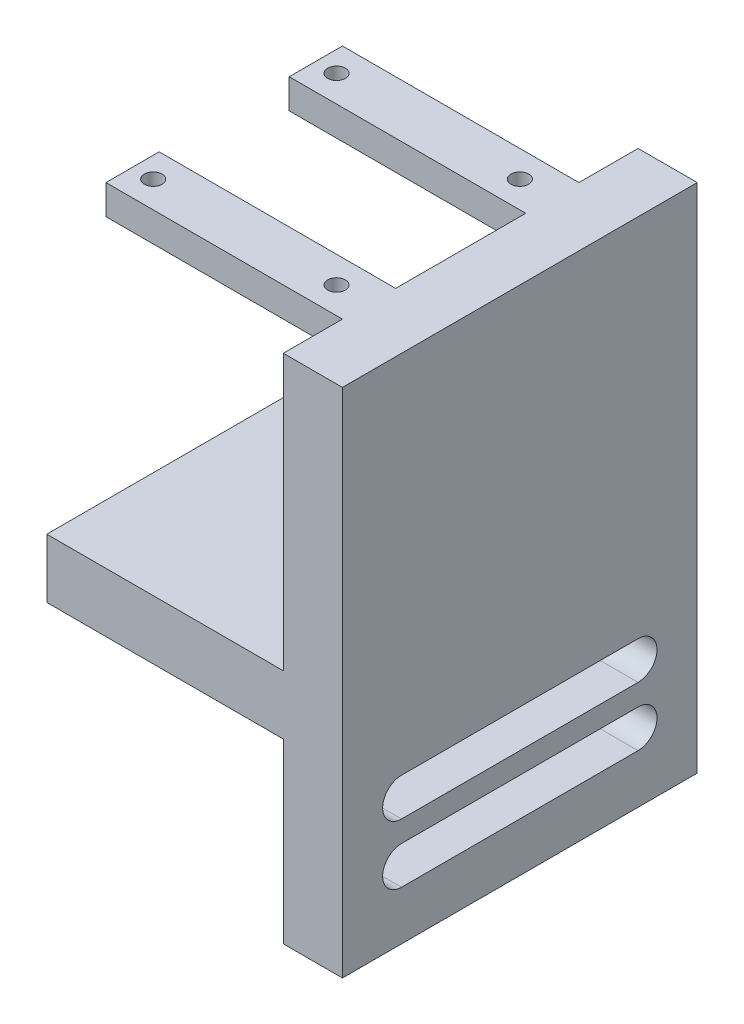
SolidWorks part; units mm, degrees
ref_plane "Front Plane" through (0, 0, 0) normal (0, 0, 1) x (1, 0, 0)
ref_plane "Top Plane" through (0, 0, 0) normal (0, 1, 0) x (1, 0, 0)
ref_plane "Right Plane" through (0, 0, 0) normal (1, 0, 0) x (0, 0, -1)
sketch "Sketch1" plane through (0, 0, 0) normal (1, 0, 0) x (0, 0, -1)
  line L0 (0, 2.75) -> (0, -2.75) construction
  line L5 (-30, 56.5) -> (30, 56.5)
  line L6 (-30, 56.5) -> (-30, 0)
  line L7 (-30, 0) -> (30, 0)
  line L8 (30, 56.5) -> (30, 0)
  line L9 (-30, 56.5) -> (30, 0) construction
  line L10 (-30, 0) -> (30, 56.5) construction
  line L11 (22, 0) -> (-22, 0) construction
  line L13 (-30, -30) -> (30, -30)
  line L14 (-30, -30) -> (-30, 0)
  line L15 (-30, 0) -> (30, 0)
  line L16 (30, -30) -> (30, 0)
  line L17 (-20, -5.3) -> (20, -5.3)
  line L18 (-20, -5.3) -> (-20, -11.7)
  line L24 (-20, -11.7) -> (20, -11.7)
  line L29 (20, -5.3) -> (20, -11.7)
  line L30 (-20, -15.3) -> (20, -15.3)
  line L31 (-20, -15.3) -> (-20, -21.7)
  line L32 (-20, -21.7) -> (20, -21.7)
  line L33 (20, -15.3) -> (20, -21.7)
  circle A2 centre (-20, -18.5) radius 3.2
  circle A3 centre (20, -18.5) radius 3.2
  circle A4 centre (-20, -8.5) radius 3.2
  circle A5 centre (20, -8.5) radius 3.2
  point P1 (0, 28.25)
  point P10 (0, -10)
  point P11 (0, -10)
  dimension "D5" = 65
  dimension "D7" = 20
  dimension "D4" = 6.4
  dimension "D1" = 56.5
  dimension "D2" = 60
  dimension "D3" = 30
  dimension "D6" = 10
extrude "Boss-Extrude1" add sketch "Sketch1" along normal blind 10
sketch "Sketch3" plane through (0, 0, 0) normal (-1, 0, 0) x (0, 0, 1)
  line L0 (30, 56.5) -> (30, -30) construction
  line L1 (-30, 10) -> (30, 10)
  line L2 (-30, 10) -> (-30, 0)
  line L3 (-30, 0) -> (30, 0)
  line L4 (30, 10) -> (30, 0)
  line L5 (-30, 10) -> (30, 0) construction
  line L6 (-30, 0) -> (30, 10) construction
  dimension "D1" = 10
  dimension "D2" = 60
extrude "Boss-Extrude2" add sketch "Sketch3" along normal blind 40
sketch "Sketch4" plane through (0, 0, 0) normal (-1, 0, 0) x (0, 0, 1)
  line L0 (30, 56.5) -> (-30, 56.5) construction
  line L17 (-20, 56.5) -> (-11, 56.5)
  line L18 (-20, 56.5) -> (-20, 51.5)
  line L19 (-20, 51.5) -> (-11, 51.5)
  line L20 (-11, 56.5) -> (-11, 51.5)
  line L21 (0, -2.75) -> (0, 2.75) construction
  line L22 (20, 51.5) -> (11, 51.5)
  line L23 (11, 56.5) -> (11, 51.5)
  line L24 (20, 56.5) -> (11, 56.5)
  line L25 (20, 56.5) -> (20, 51.5)
  dimension "D1" = 9
  dimension "D2" = 5
  dimension "D3" = 20
extrude "Boss-Extrude3" add sketch "Sketch4" along normal blind 40
sketch "Sketch5" plane through (0, 56.5, 0) normal (0, 1, 0) x (1, 0, 0)
  line L0 (0, -2.75) -> (0, 2.75) construction
  line L2 (-40, 11) -> (0, 11) construction
  line L3 (-2.75, 0) -> (2.75, 0) construction
  circle A0 centre (-5.5, 15.5) radius 1.5
  circle A1 centre (-36.5, 15.5) radius 1.5
  circle A2 centre (-5.5, -15.5) radius 1.5
  circle A3 centre (-36.5, -15.5) radius 1.5
  dimension "D2" = 3
  dimension "D4" = 3
  dimension "D1" = 5.5
  dimension "D3" = 4.5
  dimension "D5" = 31
extrude "Cut-Extrude1" cut sketch "Sketch5" against normal up to next
